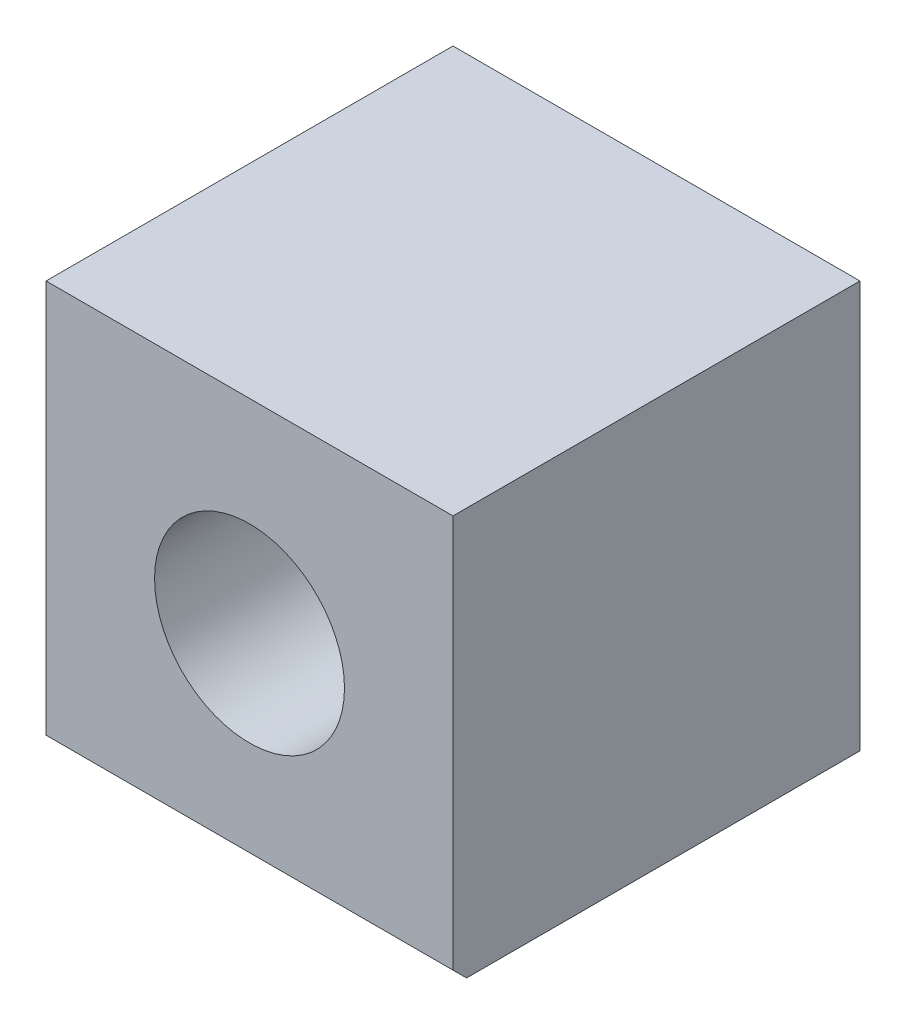
SolidWorks part; units mm, degrees
ref_plane "正面" through (0, 0, 0) normal (0, 0, 1) x (1, 0, 0)
ref_plane "平面" through (0, 0, 0) normal (0, 1, 0) x (1, 0, 0)
ref_plane "右側面" through (0, 0, 0) normal (1, 0, 0) x (0, 0, -1)
sketch "ｽｹｯﾁ1" plane through (0, 0, 0) normal (0, 0, 1) x (1, 0, 0)
  line L1 (-2.7788, 2.893) -> (3.2212, 2.893)
  line L2 (-2.7788, 2.893) -> (-2.7788, -3.107)
  line L3 (-2.7788, -3.107) -> (3.2212, -3.107)
  line L4 (3.2212, 2.893) -> (3.2212, -3.107)
  dimension "D1" = 6
  dimension "D2" = 6
extrude "ﾎﾞｽ - 押し出し1" add sketch "ｽｹｯﾁ1" along normal blind 6
sketch "ｽｹｯﾁ2" plane through (0, 0, 6) normal (0, 0, 1) x (1, 0, 0)
  line L0 (3.2212, 2.893) -> (-2.7788, 2.893) construction
  line L1 (-2.7788, 2.893) -> (-2.7788, -3.107) construction
  circle A0 centre (0.2212, -0.107) radius 1.4
  dimension "D1" = 2.8
  dimension "D2" = 3
  dimension "D3" = 3
extrude "ｶｯﾄ - 押し出し1" cut sketch "ｽｹｯﾁ2" against normal through all
sketch "ｽｹｯﾁ3" plane through (3.2212, 0, 0) normal (1, 0, 0) x (0, 0, -1)
  line L0 (-6, -3.107) -> (-6, -2.907)
  line L1 (-6, -3.107) -> (-6, 2.893) construction
  line L2 (-6, -2.907) -> (-5.8, -3.107)
  line L3 (-6, -3.107) -> (0, -3.107) construction
  line L4 (-5.8, -3.107) -> (-6, -3.107)
  dimension "D1" = 0.2
  dimension "D2" = 0.2
extrude "ｶｯﾄ - 押し出し2" cut sketch "ｽｹｯﾁ3" against normal through all
